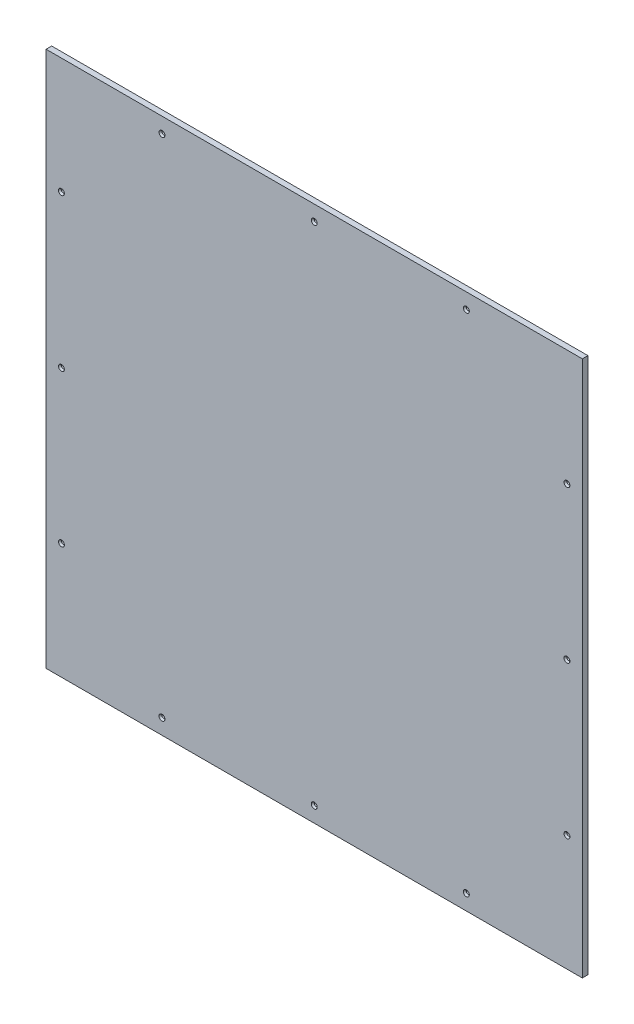
SolidWorks part; units mm, degrees
material "PE High Density"
ref_plane "Front Plane" through (0, 0, 0) normal (0, 0, 1) x (1, 0, 0)
ref_plane "Top Plane" through (0, 0, 0) normal (0, 1, 0) x (1, 0, 0)
ref_plane "Right Plane" through (0, 0, 0) normal (1, 0, 0) x (0, 0, -1)
sketch "Sketch1" plane through (0, 0, 0) normal (0, 0, 1) x (1, 0, 0)
  line L1 (-609.6, -25.4) -> (609.6, -25.4)
  line L2 (-609.6, -25.4) -> (-609.6, 1193.8)
  line L3 (-609.6, 1193.8) -> (609.6, 1193.8)
  line L4 (609.6, -25.4) -> (609.6, 1193.8)
extrude "Boss-Extrude1" add sketch "Sketch1" along normal blind 12.7 contours L1 L4 L3 L2
sketch "Sketch2" plane through (0, 0, 12.7) normal (0, 0, 1) x (1, 0, 0)
  line L1 (0, 1193.8) -> (0, -25.4) construction
  line L2 (-609.6, -25.4) -> (609.6, -25.4) construction
  line L4 (-609.6, 1193.8) -> (609.6, 1193.8) construction
  line L5 (-609.6, 584.2) -> (609.6, 584.2) construction
  line L6 (-609.6, -25.4) -> (-609.6, 1193.8) construction
  line L7 (609.6, -25.4) -> (609.6, 1193.8) construction
  circle A7 centre (-346.075, 1158.875) radius 3.302
  circle A8 centre (0.127, 1158.875) radius 3.302
  circle A9 centre (345.948, 1158.875) radius 3.302
  circle A10 centre (345.948, 9.525) radius 3.302
  circle A11 centre (0.127, 9.525) radius 3.302
  circle A12 centre (-346.075, 9.525) radius 3.302
  circle A13 centre (-574.675, 930.148) radius 3.302
  circle A14 centre (-574.675, 583.946) radius 3.302
  circle A15 centre (-574.675, 238.252) radius 3.302
  circle A16 centre (574.675, 930.148) radius 3.302
  circle A17 centre (574.675, 583.946) radius 3.302
  circle A18 centre (574.675, 238.252) radius 3.302
  dimension "D1" = 6.604
  dimension "D2" = 263.525
  dimension "D3" = 263.652
  dimension "D6" = 6.604
  dimension "D5" = 34.925
  dimension "D4" = 346.202
  dimension "D7" = 263.652
  dimension "D8" = 34.925
  dimension "D9" = 346.202
  dimension "D10" = 263.652
extrude "Cut-Extrude4" cut sketch "Sketch2" against normal blind 12.7
hole_wizard "CSK for 1/4 Flat Head Socket Cap Screw1" positions "3DSketch1" profile "Sketch3" countersink size "1/4" standard "ANSI Inch" end condition through all
sketch3d "3DSketch1"
  line L0 (345.948, 9.525, 0) -> (345.948, 9.525, 12.7) construction
  line L1 (0.127, 9.525, 0) -> (0.127, 9.525, 12.7) construction
  line L2 (-346.075, 9.525, 0) -> (-346.075, 9.525, 12.7) construction
  line L3 (-574.675, 238.252, 0) -> (-574.675, 238.252, 12.7) construction
  line L4 (-574.675, 583.946, 0) -> (-574.675, 583.946, 12.7) construction
  line L5 (-574.675, 930.148, 0) -> (-574.675, 930.148, 12.7) construction
  line L6 (-346.075, 1158.875, 0) -> (-346.075, 1158.875, 12.7) construction
  line L7 (0.127, 1158.875, 0) -> (0.127, 1158.875, 12.7) construction
  line L8 (345.948, 1158.875, 0) -> (345.948, 1158.875, 12.7) construction
  line L9 (574.675, 930.148, 0) -> (574.675, 930.148, 12.7) construction
  line L10 (574.675, 583.946, 0) -> (574.675, 583.946, 12.7) construction
  line L11 (574.675, 238.252, 0) -> (574.675, 238.252, 12.7) construction
  point P0 (345.948, 9.525, 12.7)
  point P4 (0.127, 9.525, 12.7)
  point P8 (-346.075, 9.525, 12.7)
  point P12 (-574.675, 238.252, 12.7)
  point P16 (-574.675, 583.946, 12.7)
  point P20 (-574.675, 930.148, 12.7)
  point P24 (-346.075, 1158.875, 12.7)
  point P28 (0.127, 1158.875, 12.7)
  point P32 (345.948, 1158.875, 12.7)
  point P36 (574.675, 930.148, 12.7)
  point P40 (574.675, 583.946, 12.7)
  point P44 (574.675, 238.252, 12.7)
sketch "Sketch3" plane through (345.948, 9.525, 12.7) normal (1, 0, 0) x (0, -1, 0)
  line L0 (0, 0) -> (0, 12.7)
  line L1 (0, 12.7) -> (3.5712, 12.7)
  line L2 (3.5712, 12.7) -> (3.5712, 3.6495)
  line L3 (3.5712, 3.6495) -> (6.7437, 0)
  line L5 (6.7437, 0) -> (0, 0)
  line L6 (-3.5712, 3.6495) -> (-6.7437, 0) construction
  line L11 (0, -6.35) -> (0, 107.95) construction
  dimension "Thru Hole Dia." = 7.1425
  dimension "Thru Hole Depth" = 12.7
  dimension "Near C'Sink Dia." = 13.4874
  dimension "Near C'Sink Angle" = 82
